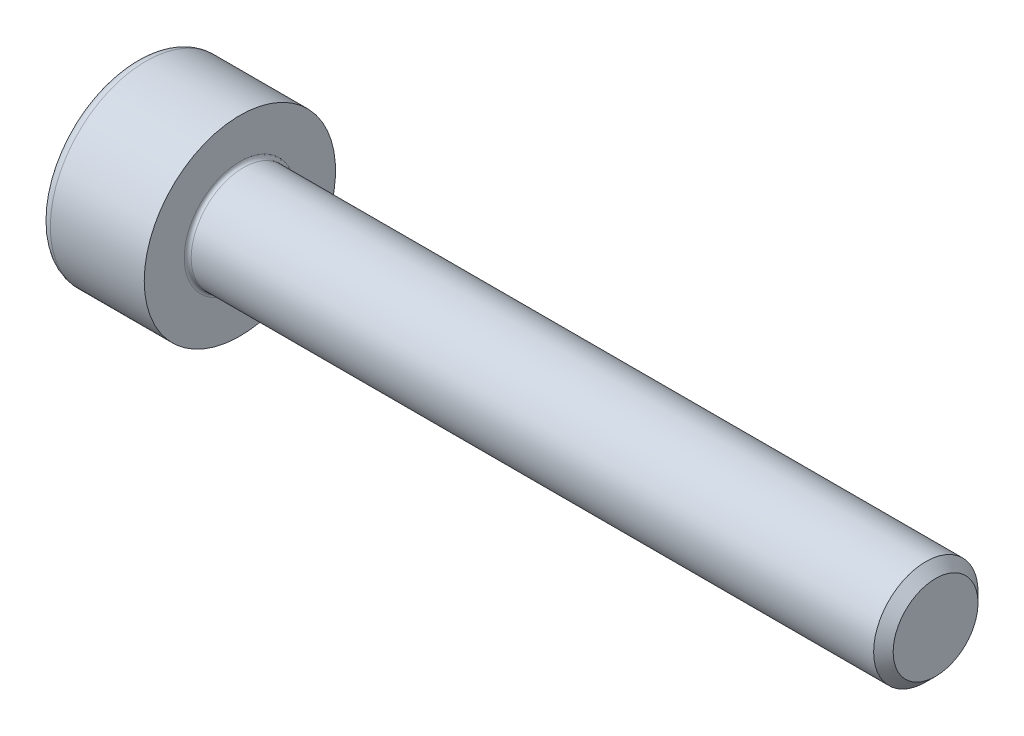
SolidWorks part; units mm, degrees
ref_plane "Plane1" through (0, 0, 0) normal (0, 0, 1) x (1, 0, 0)
ref_plane "Plane2" through (0, 0, 0) normal (0, 1, 0) x (1, 0, 0)
ref_plane "Plane3" through (0, 0, 0) normal (1, 0, 0) x (0, 0, -1)
sketch "BodySke" plane through (0, 0, 0) normal (0, 0, 1) x (1, 0, 0)
  line L0 (0, 0) -> (0, 2.75)
  line L1 (0, 2.75) -> (3, 2.75)
  line L2 (3, 2.75) -> (3, 1.5)
  line L3 (3, 1.5) -> (22.7195, 1.5)
  line L4 (23, 1.2195) -> (23, 0)
  line L5 (23, 0) -> (0, 0)
  line L6 (-31.75, 0) -> (127, 0) construction
  line L8 (23, 1.2195) -> (22.7195, 1.5)
  line L10 (23, -1.2195) -> (22.7195, -1.5) construction
  line L11 (3.5, 9.525) -> (3.5, 3.175) construction
  line L12 (3, 9.525) -> (3, 3.175) construction
  line L13 (-37, 9.525) -> (-37, 3.175) construction
  dimension "Diameter" = 3
  dimension "Head_ht" = 3
  dimension "Length" = 20
  dimension "Body_ch_ang" = 45
  dimension "Head_dia" = 5.5
  dimension "Minor_dia" = 2.439
  dimension "Advance" = 0.5
  dimension "Thread_nom" = 20
  dimension "Thread_length" = 60
revolve "Base-Revolve" add sketch "BodySke"
cosmetic thread "ThreadCosmetic" [suppressed]
fillet "Fillet1" radius 0.1 1 edges at (3, 0, 1.5)
fillet "Fillet2" radius 0.3 1 edges at (0, 0, 2.75)
sketch "Sketch2" plane through (0, 0, 0) normal (0, 0, 1) x (1, 0, 0)
  line L0 (0, 1.26) -> (1.3, 1.26)
  line L1 (1.3, 1.26) -> (2.0275, 0)
  line L2 (-31.75, 0) -> (127, 0) construction
  line L3 (2.0275, 0) -> (0, 0)
  line L4 (0, 0) -> (0, 1.26)
  line L6 (0, 0) -> (47.625, 0) construction
  dimension "D1" = 1.26
  dimension "D2" = 60
  dimension "Depth" = 1.3
revolve "Hex-PreBroach" cut sketch "Sketch2" angle 360 about L6
sketch "Sketch3" plane through (0, 0, 0) normal (-1, 0, 0) x (0, 0.5, 0.866)
  line L0 (0.7275, 1.26) -> (-0.7275, 1.26)
  line L1 (-0.7275, 1.26) -> (-1.4549, 0)
  line L2 (0.7275, 1.26) -> (1.4549, 0)
  line L3 (0.7275, -1.26) -> (1.4549, 0)
  line L4 (0.7275, -1.26) -> (-0.7275, -1.26)
  line L5 (-0.7275, -1.26) -> (-1.4549, 0)
  dimension "D1" = 1.26
  dimension "D2" = 1.26
  dimension "Hex_size" = 2.52
extrude "Hex" cut sketch "Sketch3" against normal blind 1.3
sketch "ThdSchSke" plane through (0, 0, 0) normal (0, 0, 1) x (1, 0, 0)
  line L0 (4.5, -1.2195) -> (4.3036, -1.5)
  line L1 (4.5, -1.2195) -> (4.6964, -1.5)
  line L2 (4.6964, -1.5) -> (4.6964, -1.875)
  line L3 (-3.175, 0) -> (5.1513, 0) construction
  line L4 (0, 2.45) -> (0, -2.45) construction
  line L5 (4.6964, -1.875) -> (4.3036, -1.875)
  line L6 (4.3036, -1.875) -> (4.3036, -1.5)
  dimension "Thread_minor" = 2.439
  dimension "Diameter" = 3
  dimension "Start" = 4.5
  dimension "SideAngle" = 55
  dimension "VeeAngle" = 70
  dimension "Overcut" = 3.75
revolve "ThreadSchematic" [suppressed] cut sketch "ThdSchSke" angle 360 about L3
pattern_linear "ThdSchPat" [suppressed]
equation "\"D2@Sketch3\" = \"Hex_size@Sketch3\" / 2"
equation "\"D1@Sketch3\" = \"Hex_size@Sketch3\" / 2"
equation "\"D1@Sketch2\" = \"Hex_size@Sketch3\" / 2"
equation "\"Thread_minor@ThreadCosmetic\"  =  \"Minor_dia@BodySke\""
equation "\"Depth@Sketch2\" =  \"Key_eng@Hex\""
equation "\"Thread_length@ThreadCosmetic\" = ((sgn( (\"Length@BodySke\" - \"Advance@BodySke\" * 3.0) - \"Thread_nom@BodySke\" )-1)*( (\"Length@BodySke\" - \"Advance@BodySke\" * 3.0) - \"Thread_nom@BodySke\" ))/-2+ \"Thread_nom@BodySke\""
equation "\"Thread_minor@ThdSchSke\" = \"Minor_dia@BodySke\""
equation "\"Diameter@ThdSchSke\" = \"Diameter@BodySke\""
equation "\"Overcut@ThdSchSke\" = \"Diameter@BodySke\" * 1.25"
equation "\"Start@ThdSchSke\" = \"Head_ht@BodySke\" + \"Length@BodySke\" - \"Thread_length@ThreadCosmetic\"  '---Non-countersunk---"
equation "\"Num_threads@ThdSchPat\" = int( \"Thread_length@ThreadCosmetic\" / \"Advance@BodySke\" + 0.999 )  + 1"
equation "\"Advance@ThdSchPat\" = \"Thread_length@ThreadCosmetic\" /  (\"Num_threads@ThdSchPat\" - 1) 'relax it"
equation "\"Num_threads@ThdSchPat\" = \"Num_threads@ThdSchPat\" - sgn( \"Num_threads@ThdSchPat\" - 1) '---chamfered tips only---"
